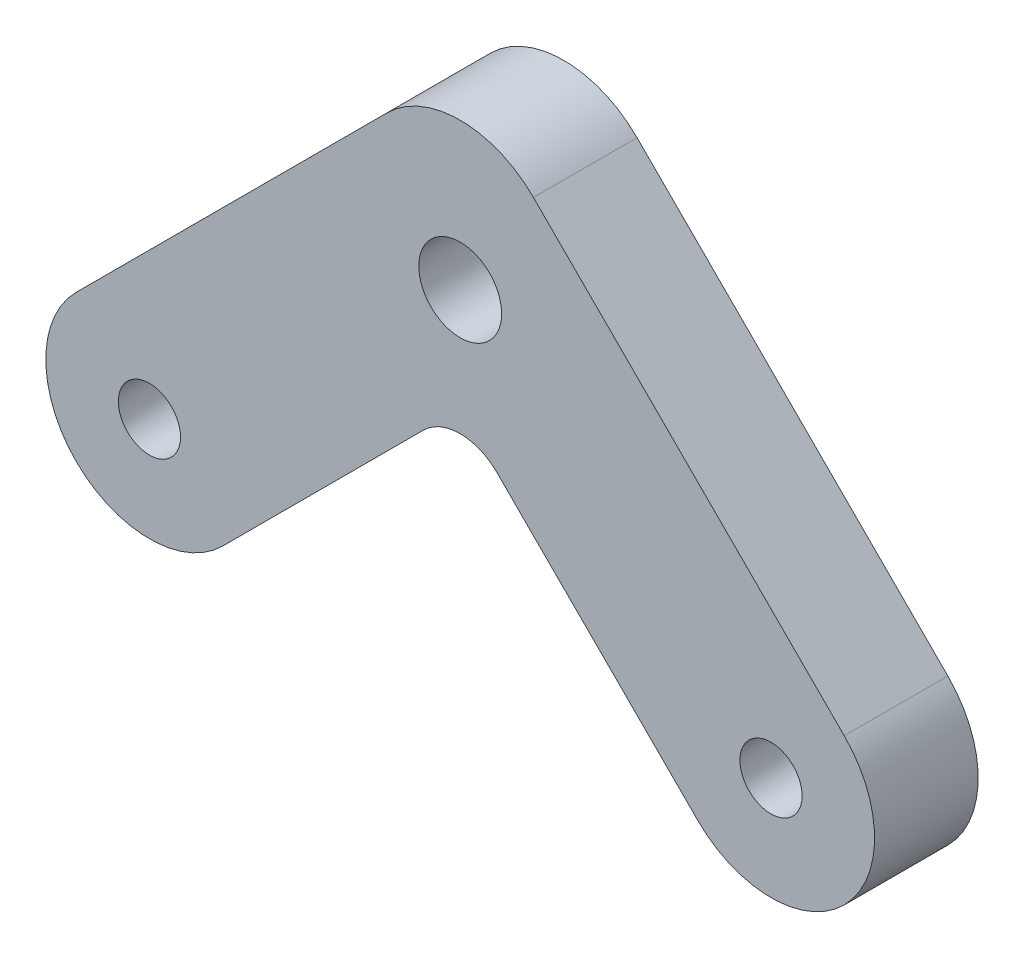
SolidWorks part; units mm, degrees
ref_plane "前视基准面" through (0, 0, 0) normal (0, 0, 1) x (1, 0, 0)
ref_plane "上视基准面" through (0, 0, 0) normal (0, 1, 0) x (1, 0, 0)
ref_plane "右视基准面" through (0, 0, 0) normal (1, 0, 0) x (0, 0, -1)
sketch "草图1" plane through (0, 0, 0) normal (0, 0, 1) x (1, 0, 0)
  line L0 (-7.0711, 11.2648) -> (-37.0711, -18.7352)
  line L1 (0, -9.9484) -> (-22.9289, -32.8774)
  line L2 (0, 28.389) -> (0, 14.1937) construction
  line L3 (0, -9.9484) -> (22.9289, -32.8774)
  line L4 (7.0711, 11.2648) -> (37.0711, -18.7352)
  line L5 (0, -9.9484) -> (0, -43.6001) construction
  arc A0 (7.0711, 11.2648) -> (-7.0711, 11.2648) centre (0, 4.1937) ccw
  arc A1 (-37.0711, -18.7352) -> (-22.9289, -32.8774) centre (-30, -25.8063) ccw
  arc A2 (37.0711, -18.7352) -> (22.9289, -32.8774) centre (30, -25.8063) cw
  dimension "D1" = 20
  dimension "D2" = 20
  dimension "D3" = 30
  dimension "D4" = 30
extrude "凸台-拉伸1" add sketch "草图1" along normal blind 10 contours L0 A1 L1 L3 A2 L4 A0
sketch "草图2" plane through (0, 0, 10) normal (0, 0, 1) x (1, 0, 0)
  circle A0 centre (0, 0) radius 4
  circle A1 centre (-30, -25.8063) radius 3
  circle A2 centre (30, -25.8063) radius 3
  dimension "D1" = 8
  dimension "D2" = 6
  dimension "D3" = 6
extrude "切除-拉伸1" cut sketch "草图2" against normal blind 10 contours A0 | A1 | A2
fillet "圆角1" radius 5 1 edges at (0, -9.9484, 5)
